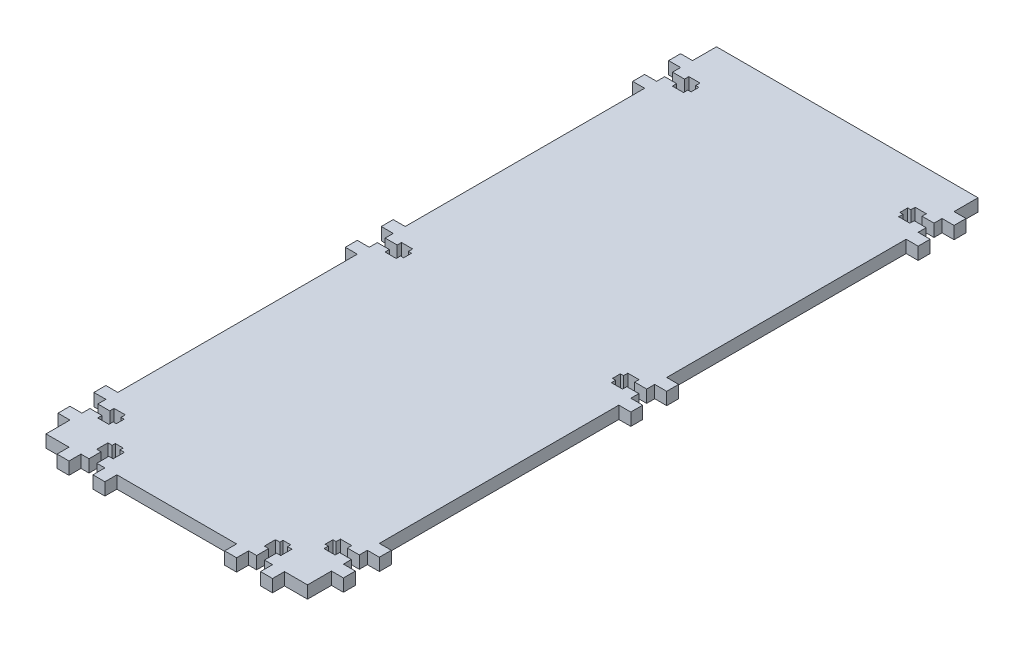
SolidWorks part; units mm, degrees
material "Acrylic (Blue)"
ref_plane "Front Plane" through (0, 0, 0) normal (0, 0, 1) x (1, 0, 0)
ref_plane "Top Plane" through (0, 0, 0) normal (0, 1, 0) x (1, 0, 0)
ref_plane "Right Plane" through (0, 0, 0) normal (1, 0, 0) x (0, 0, -1)
sketch "Sketch1" plane through (0, 0, 0) normal (0, 1, 0) x (1, 0, 0)
  line L0 (-69.342, 177.8) -> (69.342, -177.8) construction
  line L1 (-69.342, 177.8) -> (69.342, 177.8)
  line L2 (-69.342, 177.8) -> (-69.342, -177.8)
  line L3 (-69.342, -177.8) -> (69.342, -177.8)
  line L4 (69.342, 177.8) -> (69.342, -177.8)
  dimension "D1" = 138.684
  dimension "D2" = 355.6
extrude "Boss-Extrude1" add sketch "Sketch1" along normal blind 6.604
sketch "Sketch2" plane through (0, 6.604, 0) normal (0, 1, 0) x (1, 0, 0)
  line L0 (-69.342, 177.8) -> (-69.342, -177.8) construction
  line L1 (69.342, -177.8) -> (69.342, 177.8) construction
  line L2 (-69.342, -177.8) -> (69.342, -177.8) construction
  line L3 (69.342, 177.8) -> (-69.342, 177.8) construction
  line L4 (-75.692, 139.7) -> (-75.692, 12.7) construction
  line L5 (-75.692, -139.7) -> (-75.692, -12.7) construction
  line L6 (-69.342, -177.8) -> (-57.15, -177.8) construction
  line L7 (57.15, -177.8) -> (69.342, -177.8) construction
  line B0 (-69.342, 150.3172) -> (-62.992, 150.3172) construction
  line B1 (-62.992, 150.3172) -> (-62.992, 148.0312) construction
  line B2 (-62.992, 148.0312) -> (-57.0484, 148.0312) construction
  line B3 (-57.0484, 148.0312) -> (-57.0484, 150.3172) construction
  line B4 (-57.0484, 150.3172) -> (-55.372, 150.3172) construction
  line B5 (-55.372, 150.3172) -> (-55.372, 154.4828) construction
  line B6 (-55.372, 154.4828) -> (-57.0484, 154.4828) construction
  line B7 (-57.0484, 154.4828) -> (-57.0484, 156.7688) construction
  line B8 (-57.0484, 156.7688) -> (-62.992, 156.7688) construction
  line B9 (-62.992, 156.7688) -> (-62.992, 154.4828) construction
  line B10 (-62.992, 154.4828) -> (-69.342, 154.4828) construction
  line B11 (-69.342, 154.4828) -> (-69.342, 158.75) construction
  line B12 (-69.342, 158.75) -> (-75.692, 158.75) construction
  line B13 (-75.692, 158.75) -> (-75.692, 165.1) construction
  line B14 (-75.692, 165.1) -> (-69.342, 165.1) construction
  line B15 (-69.342, 150.3172) -> (-69.342, 146.05) construction
  line B16 (-69.342, 146.05) -> (-75.692, 146.05) construction
  line B17 (-75.692, 146.05) -> (-75.692, 139.7) construction
  line B18 (-75.692, 139.7) -> (-69.342, 139.7) construction
  line B19 (-69.342, 154.4828) -> (-69.342, 150.3172) construction
  line B20 (-69.342, -2.0828) -> (-62.992, -2.0828) construction
  line B21 (-62.992, -2.0828) -> (-62.992, -4.3688) construction
  line B22 (-62.992, -4.3688) -> (-57.0484, -4.3688) construction
  line B23 (-57.0484, -4.3688) -> (-57.0484, -2.0828) construction
  line B24 (-57.0484, -2.0828) -> (-55.372, -2.0828) construction
  line B25 (-55.372, -2.0828) -> (-55.372, 2.0828) construction
  line B26 (-55.372, 2.0828) -> (-57.0484, 2.0828) construction
  line B27 (-57.0484, 2.0828) -> (-57.0484, 4.3688) construction
  line B28 (-57.0484, 4.3688) -> (-62.992, 4.3688) construction
  line B29 (-62.992, 4.3688) -> (-62.992, 2.0828) construction
  line B30 (-62.992, 2.0828) -> (-69.342, 2.0828) construction
  line B31 (-69.342, 2.0828) -> (-69.342, 6.35) construction
  line B32 (-69.342, 6.35) -> (-75.692, 6.35) construction
  line B33 (-75.692, 6.35) -> (-75.692, 12.7) construction
  line B34 (-75.692, 12.7) -> (-69.342, 12.7) construction
  line B35 (-69.342, -6.35) -> (-75.692, -6.35) construction
  line B36 (-75.692, -6.35) -> (-75.692, -12.7) construction
  line B37 (-75.692, -12.7) -> (-69.342, -12.7) construction
  line B38 (-69.342, 2.0828) -> (-69.342, -2.0828) construction
  line B39 (-69.342, -154.4828) -> (-62.992, -154.4828) construction
  line B40 (-62.992, -154.4828) -> (-62.992, -156.7688) construction
  line B41 (-62.992, -156.7688) -> (-57.0484, -156.7688) construction
  line B42 (-57.0484, -156.7688) -> (-57.0484, -154.4828) construction
  line B43 (-57.0484, -154.4828) -> (-55.372, -154.4828) construction
  line B44 (-55.372, -154.4828) -> (-55.372, -150.3172) construction
  line B45 (-55.372, -150.3172) -> (-57.0484, -150.3172) construction
  line B46 (-57.0484, -150.3172) -> (-57.0484, -148.0312) construction
  line B47 (-57.0484, -148.0312) -> (-62.992, -148.0312) construction
  line B48 (-62.992, -148.0312) -> (-62.992, -150.3172) construction
  line B49 (-62.992, -150.3172) -> (-69.342, -150.3172) construction
  line B50 (-69.342, -150.3172) -> (-69.342, -146.05) construction
  line B51 (-69.342, -146.05) -> (-75.692, -146.05) construction
  line B52 (-75.692, -146.05) -> (-75.692, -139.7) construction
  line B53 (-75.692, -139.7) -> (-69.342, -139.7) construction
  line B54 (-69.342, -154.4828) -> (-69.342, -158.75) construction
  line B55 (-69.342, -158.75) -> (-75.692, -158.75) construction
  line B56 (-75.692, -158.75) -> (-75.692, -165.1) construction
  line B57 (-75.692, -165.1) -> (-69.342, -165.1) construction
  line B58 (-69.342, -150.3172) -> (-69.342, -154.4828) construction
  line B59 (69.342, 154.4828) -> (62.992, 154.4828) construction
  line B60 (62.992, 154.4828) -> (62.992, 156.7688) construction
  line B61 (62.992, 156.7688) -> (57.0484, 156.7688) construction
  line B62 (57.0484, 156.7688) -> (57.0484, 154.4828) construction
  line B63 (57.0484, 154.4828) -> (55.372, 154.4828) construction
  line B64 (55.372, 154.4828) -> (55.372, 150.3172) construction
  line B65 (55.372, 150.3172) -> (57.0484, 150.3172) construction
  line B66 (57.0484, 150.3172) -> (57.0484, 148.0312) construction
  line B67 (57.0484, 148.0312) -> (62.992, 148.0312) construction
  line B68 (62.992, 148.0312) -> (62.992, 150.3172) construction
  line B69 (62.992, 150.3172) -> (69.342, 150.3172) construction
  line B70 (69.342, 146.05) -> (75.692, 146.05) construction
  line B71 (75.692, 146.05) -> (75.692, 139.7) construction
  line B72 (75.692, 139.7) -> (69.342, 139.7) construction
  line B73 (69.342, 158.75) -> (75.692, 158.75) construction
  line B74 (75.692, 158.75) -> (75.692, 165.1) construction
  line B75 (75.692, 165.1) -> (69.342, 165.1) construction
  line B76 (69.342, 150.3172) -> (69.342, 154.4828) construction
  line B77 (69.342, 2.0828) -> (62.992, 2.0828) construction
  line B78 (62.992, 2.0828) -> (62.992, 4.3688) construction
  line B79 (62.992, 4.3688) -> (57.0484, 4.3688) construction
  line B80 (57.0484, 4.3688) -> (57.0484, 2.0828) construction
  line B81 (57.0484, 2.0828) -> (55.372, 2.0828) construction
  line B82 (55.372, 2.0828) -> (55.372, -2.0828) construction
  line B83 (55.372, -2.0828) -> (57.0484, -2.0828) construction
  line B84 (57.0484, -2.0828) -> (57.0484, -4.3688) construction
  line B85 (57.0484, -4.3688) -> (62.992, -4.3688) construction
  line B86 (62.992, -4.3688) -> (62.992, -2.0828) construction
  line B87 (62.992, -2.0828) -> (69.342, -2.0828) construction
  line B88 (69.342, -6.35) -> (75.692, -6.35) construction
  line B89 (75.692, -6.35) -> (75.692, -12.7) construction
  line B90 (75.692, -12.7) -> (69.342, -12.7) construction
  line B91 (69.342, 2.0828) -> (69.342, 6.35) construction
  line B92 (69.342, 6.35) -> (75.692, 6.35) construction
  line B93 (75.692, 6.35) -> (75.692, 12.7) construction
  line B94 (75.692, 12.7) -> (69.342, 12.7) construction
  line B95 (69.342, -2.0828) -> (69.342, 2.0828) construction
  line B96 (69.342, -150.3172) -> (62.992, -150.3172) construction
  line B97 (62.992, -150.3172) -> (62.992, -148.0312) construction
  line B98 (62.992, -148.0312) -> (57.0484, -148.0312) construction
  line B99 (57.0484, -148.0312) -> (57.0484, -150.3172) construction
  line B100 (57.0484, -150.3172) -> (55.372, -150.3172) construction
  line B101 (55.372, -150.3172) -> (55.372, -154.4828) construction
  line B102 (55.372, -154.4828) -> (57.0484, -154.4828) construction
  line B103 (57.0484, -154.4828) -> (57.0484, -156.7688) construction
  line B104 (57.0484, -156.7688) -> (62.992, -156.7688) construction
  line B105 (62.992, -156.7688) -> (62.992, -154.4828) construction
  line B106 (62.992, -154.4828) -> (69.342, -154.4828) construction
  line B107 (69.342, -154.4828) -> (69.342, -158.75) construction
  line B108 (69.342, -158.75) -> (75.692, -158.75) construction
  line B109 (75.692, -158.75) -> (75.692, -165.1) construction
  line B110 (75.692, -165.1) -> (69.342, -165.1) construction
  line B111 (69.342, -146.05) -> (75.692, -146.05) construction
  line B112 (75.692, -146.05) -> (75.692, -139.7) construction
  line B113 (75.692, -139.7) -> (69.342, -139.7) construction
  line B114 (69.342, -154.4828) -> (69.342, -150.3172) construction
  line B115 (46.5328, -177.8) -> (46.5328, -171.45) construction
  line B116 (46.5328, -171.45) -> (48.8188, -171.45) construction
  line B117 (48.8188, -171.45) -> (48.8188, -165.5064) construction
  line B118 (48.8188, -165.5064) -> (46.5328, -165.5064) construction
  line B119 (46.5328, -165.5064) -> (46.5328, -163.83) construction
  line B120 (46.5328, -163.83) -> (42.3672, -163.83) construction
  line B121 (42.3672, -163.83) -> (42.3672, -165.5064) construction
  line B122 (42.3672, -165.5064) -> (40.0812, -165.5064) construction
  line B123 (40.0812, -165.5064) -> (40.0812, -171.45) construction
  line B124 (40.0812, -171.45) -> (42.3672, -171.45) construction
  line B125 (42.3672, -171.45) -> (42.3672, -177.8) construction
  line B126 (42.3672, -177.8) -> (38.1, -177.8) construction
  line B127 (38.1, -177.8) -> (38.1, -184.15) construction
  line B128 (38.1, -184.15) -> (31.75, -184.15) construction
  line B129 (31.75, -184.15) -> (31.75, -177.8) construction
  line B130 (50.8, -177.8) -> (50.8, -184.15) construction
  line B131 (50.8, -184.15) -> (57.15, -184.15) construction
  line B132 (57.15, -184.15) -> (57.15, -177.8) construction
  line B133 (42.3672, -177.8) -> (46.5328, -177.8) construction
  line B134 (-42.3672, -177.8) -> (-42.3672, -171.45) construction
  line B135 (-42.3672, -171.45) -> (-40.0812, -171.45) construction
  line B136 (-40.0812, -171.45) -> (-40.0812, -165.5064) construction
  line B137 (-40.0812, -165.5064) -> (-42.3672, -165.5064) construction
  line B138 (-42.3672, -165.5064) -> (-42.3672, -163.83) construction
  line B139 (-42.3672, -163.83) -> (-46.5328, -163.83) construction
  line B140 (-46.5328, -163.83) -> (-46.5328, -165.5064) construction
  line B141 (-46.5328, -165.5064) -> (-48.8188, -165.5064) construction
  line B142 (-48.8188, -165.5064) -> (-48.8188, -171.45) construction
  line B143 (-48.8188, -171.45) -> (-46.5328, -171.45) construction
  line B144 (-46.5328, -171.45) -> (-46.5328, -177.8) construction
  line B145 (-46.5328, -177.8) -> (-50.8, -177.8) construction
  line B146 (-50.8, -177.8) -> (-50.8, -184.15) construction
  line B147 (-50.8, -184.15) -> (-57.15, -184.15) construction
  line B148 (-57.15, -184.15) -> (-57.15, -177.8) construction
  line B149 (-42.3672, -177.8) -> (-38.1, -177.8) construction
  line B150 (-38.1, -177.8) -> (-38.1, -184.15) construction
  line B151 (-38.1, -184.15) -> (-31.75, -184.15) construction
  line B152 (-31.75, -184.15) -> (-31.75, -177.8) construction
  line B153 (-46.5328, -177.8) -> (-42.3672, -177.8) construction
  dimension "D1" = 88.9
  dimension "D2" = 12.7
  dimension "D4" = 12.7
sketch_block_instance "NUT_HOLE-1"
sketch_block "NUT_HOLE" parameters "D1"=6.35, "D2"=4.1656, "D3"=25.4, "D4"=6.35, "D5"=8.7376, "D6"=5.9436, "D7"=6.35, "D8"=20.32
sketch_block_instance "NUT_HOLE-2"
sketch_block_instance "NUT_HOLE-3"
sketch_block_instance "NUT_HOLE-4"
sketch_block_instance "NUT_HOLE-5"
sketch_block_instance "NUT_HOLE-6"
sketch_block_instance "NUT_HOLE-8"
sketch_block_instance "NUT_HOLE-9"
sketch "Sketch4" plane through (0, 6.604, 0) normal (0, 1, 0) x (1, 0, 0)
  line L0 (-62.992, 154.4828) -> (-69.342, 154.4828) construction
  line L1 (-62.992, 156.7688) -> (-62.992, 154.4828) construction
  line L2 (-57.0484, 156.7688) -> (-62.992, 156.7688) construction
  line L3 (-57.0484, 154.4828) -> (-57.0484, 156.7688) construction
  line L4 (-55.372, 154.4828) -> (-57.0484, 154.4828) construction
  line L5 (-55.372, 150.3172) -> (-55.372, 154.4828) construction
  line L6 (-57.0484, 150.3172) -> (-55.372, 150.3172) construction
  line L7 (-62.992, 148.0312) -> (-57.0484, 148.0312) construction
  line L8 (-69.342, 150.3172) -> (-62.992, 150.3172) construction
  line L9 (-62.992, 150.3172) -> (-62.992, 148.0312) construction
  line L10 (-57.0484, 148.0312) -> (-57.0484, 150.3172) construction
  line L11 (57.0484, 154.4828) -> (55.372, 154.4828) construction
  line L12 (57.0484, 156.7688) -> (57.0484, 154.4828) construction
  line L13 (62.992, 156.7688) -> (57.0484, 156.7688) construction
  line L14 (62.992, 154.4828) -> (62.992, 156.7688) construction
  line L15 (69.342, 154.4828) -> (62.992, 154.4828) construction
  line L16 (62.992, 150.3172) -> (69.342, 150.3172) construction
  line L17 (62.992, 148.0312) -> (62.992, 150.3172) construction
  line L18 (57.0484, 148.0312) -> (62.992, 148.0312) construction
  line L19 (55.372, 150.3172) -> (57.0484, 150.3172) construction
  line L20 (57.0484, 150.3172) -> (57.0484, 148.0312) construction
  line L21 (55.372, 154.4828) -> (55.372, 150.3172) construction
  line L22 (-62.992, 154.4828) -> (-69.342, 154.4828)
  line L23 (-62.992, 156.7688) -> (-62.992, 154.4828)
  line L24 (-57.0484, 156.7688) -> (-62.992, 156.7688)
  line L25 (-57.0484, 154.4828) -> (-57.0484, 156.7688)
  line L26 (-55.372, 154.4828) -> (-57.0484, 154.4828)
  line L27 (-55.372, 150.3172) -> (-55.372, 154.4828)
  line L28 (-57.0484, 150.3172) -> (-55.372, 150.3172)
  line L29 (-62.992, 148.0312) -> (-57.0484, 148.0312)
  line L30 (-69.342, 150.3172) -> (-62.992, 150.3172)
  line L31 (-62.992, 150.3172) -> (-62.992, 148.0312)
  line L32 (-57.0484, 148.0312) -> (-57.0484, 150.3172)
  line L33 (57.0484, 154.4828) -> (55.372, 154.4828)
  line L34 (57.0484, 156.7688) -> (57.0484, 154.4828)
  line L35 (62.992, 156.7688) -> (57.0484, 156.7688)
  line L36 (62.992, 154.4828) -> (62.992, 156.7688)
  line L37 (69.342, 154.4828) -> (62.992, 154.4828)
  line L38 (62.992, 150.3172) -> (69.342, 150.3172)
  line L39 (62.992, 148.0312) -> (62.992, 150.3172)
  line L40 (57.0484, 148.0312) -> (62.992, 148.0312)
  line L41 (55.372, 150.3172) -> (57.0484, 150.3172)
  line L42 (57.0484, 150.3172) -> (57.0484, 148.0312)
  line L43 (55.372, 154.4828) -> (55.372, 150.3172)
  line L44 (-62.992, 2.0828) -> (-69.342, 2.0828) construction
  line L45 (-62.992, 4.3688) -> (-62.992, 2.0828) construction
  line L46 (-57.0484, 4.3688) -> (-62.992, 4.3688) construction
  line L47 (-57.0484, 2.0828) -> (-57.0484, 4.3688) construction
  line L48 (-55.372, 2.0828) -> (-57.0484, 2.0828) construction
  line L49 (-55.372, -2.0828) -> (-55.372, 2.0828) construction
  line L50 (-57.0484, -2.0828) -> (-55.372, -2.0828) construction
  line L51 (-62.992, -4.3688) -> (-57.0484, -4.3688) construction
  line L52 (-57.0484, -4.3688) -> (-57.0484, -2.0828) construction
  line L53 (-62.992, -2.0828) -> (-62.992, -4.3688) construction
  line L54 (-69.342, -2.0828) -> (-62.992, -2.0828) construction
  line L55 (69.342, 2.0828) -> (62.992, 2.0828) construction
  line L56 (62.992, 2.0828) -> (62.992, 4.3688) construction
  line L57 (62.992, 4.3688) -> (57.0484, 4.3688) construction
  line L58 (57.0484, 4.3688) -> (57.0484, 2.0828) construction
  line L59 (57.0484, 2.0828) -> (55.372, 2.0828) construction
  line L60 (55.372, 2.0828) -> (55.372, -2.0828) construction
  line L61 (55.372, -2.0828) -> (57.0484, -2.0828) construction
  line L62 (57.0484, -2.0828) -> (57.0484, -4.3688) construction
  line L63 (57.0484, -4.3688) -> (62.992, -4.3688) construction
  line L64 (62.992, -2.0828) -> (69.342, -2.0828) construction
  line L65 (62.992, -4.3688) -> (62.992, -2.0828) construction
  line L66 (-62.992, 2.0828) -> (-69.342, 2.0828)
  line L67 (-62.992, 4.3688) -> (-62.992, 2.0828)
  line L68 (-57.0484, 4.3688) -> (-62.992, 4.3688)
  line L69 (-57.0484, 2.0828) -> (-57.0484, 4.3688)
  line L70 (-55.372, 2.0828) -> (-57.0484, 2.0828)
  line L71 (-55.372, -2.0828) -> (-55.372, 2.0828)
  line L72 (-57.0484, -2.0828) -> (-55.372, -2.0828)
  line L73 (-62.992, -4.3688) -> (-57.0484, -4.3688)
  line L74 (-57.0484, -4.3688) -> (-57.0484, -2.0828)
  line L75 (-62.992, -2.0828) -> (-62.992, -4.3688)
  line L76 (-69.342, -2.0828) -> (-62.992, -2.0828)
  line L77 (69.342, 2.0828) -> (62.992, 2.0828)
  line L78 (62.992, 2.0828) -> (62.992, 4.3688)
  line L79 (62.992, 4.3688) -> (57.0484, 4.3688)
  line L80 (57.0484, 4.3688) -> (57.0484, 2.0828)
  line L81 (57.0484, 2.0828) -> (55.372, 2.0828)
  line L82 (55.372, 2.0828) -> (55.372, -2.0828)
  line L83 (55.372, -2.0828) -> (57.0484, -2.0828)
  line L84 (57.0484, -2.0828) -> (57.0484, -4.3688)
  line L85 (57.0484, -4.3688) -> (62.992, -4.3688)
  line L86 (62.992, -2.0828) -> (69.342, -2.0828)
  line L87 (62.992, -4.3688) -> (62.992, -2.0828)
  line L88 (-62.992, -150.3172) -> (-69.342, -150.3172) construction
  line L89 (-62.992, -148.0312) -> (-62.992, -150.3172) construction
  line L90 (-57.0484, -148.0312) -> (-62.992, -148.0312) construction
  line L91 (-57.0484, -150.3172) -> (-57.0484, -148.0312) construction
  line L92 (-55.372, -154.4828) -> (-55.372, -150.3172) construction
  line L93 (-55.372, -150.3172) -> (-57.0484, -150.3172) construction
  line L94 (-57.0484, -154.4828) -> (-55.372, -154.4828) construction
  line L95 (-57.0484, -156.7688) -> (-57.0484, -154.4828) construction
  line L96 (-62.992, -156.7688) -> (-57.0484, -156.7688) construction
  line L97 (-62.992, -154.4828) -> (-62.992, -156.7688) construction
  line L98 (-69.342, -154.4828) -> (-62.992, -154.4828) construction
  line L99 (69.342, -150.3172) -> (62.992, -150.3172) construction
  line L100 (62.992, -150.3172) -> (62.992, -148.0312) construction
  line L101 (62.992, -148.0312) -> (57.0484, -148.0312) construction
  line L102 (57.0484, -148.0312) -> (57.0484, -150.3172) construction
  line L103 (57.0484, -150.3172) -> (55.372, -150.3172) construction
  line L104 (55.372, -150.3172) -> (55.372, -154.4828) construction
  line L105 (55.372, -154.4828) -> (57.0484, -154.4828) construction
  line L106 (57.0484, -154.4828) -> (57.0484, -156.7688) construction
  line L107 (57.0484, -156.7688) -> (62.992, -156.7688) construction
  line L108 (62.992, -154.4828) -> (69.342, -154.4828) construction
  line L109 (62.992, -156.7688) -> (62.992, -154.4828) construction
  line L110 (-62.992, -150.3172) -> (-69.342, -150.3172)
  line L111 (-62.992, -148.0312) -> (-62.992, -150.3172)
  line L112 (-57.0484, -148.0312) -> (-62.992, -148.0312)
  line L113 (-57.0484, -150.3172) -> (-57.0484, -148.0312)
  line L114 (-55.372, -154.4828) -> (-55.372, -150.3172)
  line L115 (-55.372, -150.3172) -> (-57.0484, -150.3172)
  line L116 (-57.0484, -154.4828) -> (-55.372, -154.4828)
  line L117 (-57.0484, -156.7688) -> (-57.0484, -154.4828)
  line L118 (-62.992, -156.7688) -> (-57.0484, -156.7688)
  line L119 (-62.992, -154.4828) -> (-62.992, -156.7688)
  line L120 (-69.342, -154.4828) -> (-62.992, -154.4828)
  line L121 (69.342, -150.3172) -> (62.992, -150.3172)
  line L122 (62.992, -150.3172) -> (62.992, -148.0312)
  line L123 (62.992, -148.0312) -> (57.0484, -148.0312)
  line L124 (57.0484, -148.0312) -> (57.0484, -150.3172)
  line L125 (57.0484, -150.3172) -> (55.372, -150.3172)
  line L126 (55.372, -150.3172) -> (55.372, -154.4828)
  line L127 (55.372, -154.4828) -> (57.0484, -154.4828)
  line L128 (57.0484, -154.4828) -> (57.0484, -156.7688)
  line L129 (57.0484, -156.7688) -> (62.992, -156.7688)
  line L130 (62.992, -154.4828) -> (69.342, -154.4828)
  line L131 (62.992, -156.7688) -> (62.992, -154.4828)
  line L132 (69.342, -150.3172) -> (69.342, -154.4828)
  line L133 (69.342, 2.0828) -> (69.342, -2.0828)
  line L134 (69.342, 154.4828) -> (69.342, 150.3172)
  line L135 (-69.342, 154.4828) -> (-69.342, 150.3172)
  line L136 (-69.342, 2.0828) -> (-69.342, -2.0828)
  line L137 (-69.342, -150.3172) -> (-69.342, -154.4828)
  line L138 (-46.5328, -165.5064) -> (-48.8188, -165.5064) construction
  line L139 (-42.3672, -163.83) -> (-46.5328, -163.83) construction
  line L140 (-40.0812, -165.5064) -> (-42.3672, -165.5064) construction
  line L141 (-46.5328, -163.83) -> (-46.5328, -165.5064) construction
  line L142 (-42.3672, -165.5064) -> (-42.3672, -163.83) construction
  line L143 (-48.8188, -171.45) -> (-46.5328, -171.45) construction
  line L144 (-48.8188, -165.5064) -> (-48.8188, -171.45) construction
  line L145 (-46.5328, -171.45) -> (-46.5328, -177.8) construction
  line L146 (-42.3672, -171.45) -> (-40.0812, -171.45) construction
  line L147 (-40.0812, -171.45) -> (-40.0812, -165.5064) construction
  line L148 (-42.3672, -177.8) -> (-42.3672, -171.45) construction
  line L149 (-46.5328, -165.5064) -> (-48.8188, -165.5064)
  line L150 (-42.3672, -163.83) -> (-46.5328, -163.83)
  line L151 (-40.0812, -165.5064) -> (-42.3672, -165.5064)
  line L152 (-46.5328, -163.83) -> (-46.5328, -165.5064)
  line L153 (-42.3672, -165.5064) -> (-42.3672, -163.83)
  line L154 (-48.8188, -171.45) -> (-46.5328, -171.45)
  line L155 (-48.8188, -165.5064) -> (-48.8188, -171.45)
  line L156 (-46.5328, -171.45) -> (-46.5328, -177.8)
  line L157 (-42.3672, -171.45) -> (-40.0812, -171.45)
  line L158 (-40.0812, -171.45) -> (-40.0812, -165.5064)
  line L159 (-42.3672, -177.8) -> (-42.3672, -171.45)
  line L160 (-46.5328, -177.8) -> (-42.3672, -177.8)
  line L161 (48.8188, -165.5064) -> (46.5328, -165.5064) construction
  line L162 (46.5328, -165.5064) -> (46.5328, -163.83) construction
  line L163 (46.5328, -163.83) -> (42.3672, -163.83) construction
  line L164 (42.3672, -163.83) -> (42.3672, -165.5064) construction
  line L165 (42.3672, -165.5064) -> (40.0812, -165.5064) construction
  line L166 (40.0812, -165.5064) -> (40.0812, -171.45) construction
  line L167 (40.0812, -171.45) -> (42.3672, -171.45) construction
  line L168 (42.3672, -171.45) -> (42.3672, -177.8) construction
  line L169 (46.5328, -177.8) -> (46.5328, -171.45) construction
  line L170 (46.5328, -171.45) -> (48.8188, -171.45) construction
  line L171 (48.8188, -171.45) -> (48.8188, -165.5064) construction
  line L172 (48.8188, -165.5064) -> (46.5328, -165.5064)
  line L173 (46.5328, -165.5064) -> (46.5328, -163.83)
  line L174 (46.5328, -163.83) -> (42.3672, -163.83)
  line L175 (42.3672, -163.83) -> (42.3672, -165.5064)
  line L176 (42.3672, -165.5064) -> (40.0812, -165.5064)
  line L177 (40.0812, -165.5064) -> (40.0812, -171.45)
  line L178 (40.0812, -171.45) -> (42.3672, -171.45)
  line L179 (42.3672, -171.45) -> (42.3672, -177.8)
  line L180 (46.5328, -177.8) -> (46.5328, -171.45)
  line L181 (46.5328, -171.45) -> (48.8188, -171.45)
  line L182 (48.8188, -171.45) -> (48.8188, -165.5064)
  line L183 (42.3672, -177.8) -> (46.5328, -177.8)
extrude "Cut-Extrude1" cut sketch "Sketch4" against normal through all
sketch "Sketch5" plane through (0, 6.604, 0) normal (0, 1, 0) x (1, 0, 0)
  line L0 (-75.692, 165.1) -> (-69.342, 165.1) construction
  line L1 (-75.692, 158.75) -> (-75.692, 165.1) construction
  line L2 (-69.342, 158.75) -> (-75.692, 158.75) construction
  line L3 (-69.342, 146.05) -> (-75.692, 146.05) construction
  line L4 (-75.692, 139.7) -> (-69.342, 139.7) construction
  line L5 (-75.692, 146.05) -> (-75.692, 139.7) construction
  line L6 (75.692, 165.1) -> (69.342, 165.1) construction
  line L7 (75.692, 158.75) -> (75.692, 165.1) construction
  line L8 (69.342, 158.75) -> (75.692, 158.75) construction
  line L9 (69.342, 146.05) -> (75.692, 146.05) construction
  line L10 (75.692, 146.05) -> (75.692, 139.7) construction
  line L11 (75.692, 139.7) -> (69.342, 139.7) construction
  line L12 (-75.692, 12.7) -> (-69.342, 12.7) construction
  line L13 (-69.342, 6.35) -> (-75.692, 6.35) construction
  line L14 (-75.692, -6.35) -> (-75.692, -12.7) construction
  line L15 (-75.692, -12.7) -> (-69.342, -12.7) construction
  line L16 (-69.342, -6.35) -> (-75.692, -6.35) construction
  line L17 (-75.692, 6.35) -> (-75.692, 12.7) construction
  line L18 (-75.692, -139.7) -> (-69.342, -139.7) construction
  line L19 (-75.692, -146.05) -> (-75.692, -139.7) construction
  line L20 (-69.342, -158.75) -> (-75.692, -158.75) construction
  line L21 (-75.692, -158.75) -> (-75.692, -165.1) construction
  line L22 (-75.692, -165.1) -> (-69.342, -165.1) construction
  line L23 (-69.342, -146.05) -> (-75.692, -146.05) construction
  line L24 (75.692, -165.1) -> (69.342, -165.1) construction
  line L25 (69.342, -158.75) -> (75.692, -158.75) construction
  line L26 (75.692, -158.75) -> (75.692, -165.1) construction
  line L27 (69.342, -146.05) -> (75.692, -146.05) construction
  line L28 (75.692, -146.05) -> (75.692, -139.7) construction
  line L29 (75.692, -139.7) -> (69.342, -139.7) construction
  line L30 (75.692, -12.7) -> (69.342, -12.7) construction
  line L31 (75.692, -6.35) -> (75.692, -12.7) construction
  line L32 (69.342, -6.35) -> (75.692, -6.35) construction
  line L33 (69.342, 6.35) -> (75.692, 6.35) construction
  line L34 (75.692, 6.35) -> (75.692, 12.7) construction
  line L35 (75.692, 12.7) -> (69.342, 12.7) construction
  line L36 (-75.692, 165.1) -> (-69.342, 165.1)
  line L37 (-75.692, 158.75) -> (-75.692, 165.1)
  line L38 (-69.342, 158.75) -> (-75.692, 158.75)
  line L39 (-69.342, 146.05) -> (-75.692, 146.05)
  line L40 (-75.692, 139.7) -> (-69.342, 139.7)
  line L41 (-75.692, 146.05) -> (-75.692, 139.7)
  line L42 (75.692, 165.1) -> (69.342, 165.1)
  line L43 (75.692, 158.75) -> (75.692, 165.1)
  line L44 (69.342, 158.75) -> (75.692, 158.75)
  line L45 (69.342, 146.05) -> (75.692, 146.05)
  line L46 (75.692, 146.05) -> (75.692, 139.7)
  line L47 (75.692, 139.7) -> (69.342, 139.7)
  line L48 (-75.692, 12.7) -> (-69.342, 12.7)
  line L49 (-69.342, 6.35) -> (-75.692, 6.35)
  line L50 (-75.692, -6.35) -> (-75.692, -12.7)
  line L51 (-75.692, -12.7) -> (-69.342, -12.7)
  line L52 (-69.342, -6.35) -> (-75.692, -6.35)
  line L53 (-75.692, 6.35) -> (-75.692, 12.7)
  line L54 (-75.692, -139.7) -> (-69.342, -139.7)
  line L55 (-75.692, -146.05) -> (-75.692, -139.7)
  line L56 (-69.342, -158.75) -> (-75.692, -158.75)
  line L57 (-75.692, -158.75) -> (-75.692, -165.1)
  line L58 (-75.692, -165.1) -> (-69.342, -165.1)
  line L59 (-69.342, -146.05) -> (-75.692, -146.05)
  line L60 (75.692, -165.1) -> (69.342, -165.1)
  line L61 (69.342, -158.75) -> (75.692, -158.75)
  line L62 (75.692, -158.75) -> (75.692, -165.1)
  line L63 (69.342, -146.05) -> (75.692, -146.05)
  line L64 (75.692, -146.05) -> (75.692, -139.7)
  line L65 (75.692, -139.7) -> (69.342, -139.7)
  line L66 (75.692, -12.7) -> (69.342, -12.7)
  line L67 (75.692, -6.35) -> (75.692, -12.7)
  line L68 (69.342, -6.35) -> (75.692, -6.35)
  line L69 (69.342, 6.35) -> (75.692, 6.35)
  line L70 (75.692, 6.35) -> (75.692, 12.7)
  line L71 (75.692, 12.7) -> (69.342, 12.7)
  line L72 (69.342, 165.1) -> (69.342, 158.75)
  line L73 (69.342, 146.05) -> (69.342, 139.7)
  line L74 (69.342, 12.7) -> (69.342, 6.35)
  line L75 (69.342, -6.35) -> (69.342, -12.7)
  line L76 (69.342, -139.7) -> (69.342, -146.05)
  line L77 (69.342, -158.75) -> (69.342, -165.1)
  line L78 (-57.15, -177.8) -> (-50.8, -177.8)
  line L79 (-69.342, -165.1) -> (-69.342, -158.75)
  line L80 (-69.342, -146.05) -> (-69.342, -139.7)
  line L81 (-69.342, -6.35) -> (-69.342, -12.7)
  line L82 (-69.342, 12.7) -> (-69.342, 6.35)
  line L83 (-69.342, 146.05) -> (-69.342, 139.7)
  line L84 (-69.342, 165.1) -> (-69.342, 158.75)
  line L85 (-38.1, -177.8) -> (-31.75, -177.8)
  line L86 (31.75, -177.8) -> (38.1, -177.8)
  line L87 (50.8, -177.8) -> (57.15, -177.8)
  line L88 (57.15, -184.15) -> (57.15, -177.8) construction
  line L89 (50.8, -184.15) -> (57.15, -184.15) construction
  line L90 (50.8, -177.8) -> (50.8, -184.15) construction
  line L91 (38.1, -177.8) -> (38.1, -184.15) construction
  line L92 (38.1, -184.15) -> (31.75, -184.15) construction
  line L93 (31.75, -184.15) -> (31.75, -177.8) construction
  line L94 (-57.15, -184.15) -> (-57.15, -177.8) construction
  line L95 (-50.8, -177.8) -> (-50.8, -184.15) construction
  line L96 (-50.8, -184.15) -> (-57.15, -184.15) construction
  line L97 (-38.1, -177.8) -> (-38.1, -184.15) construction
  line L98 (-38.1, -184.15) -> (-31.75, -184.15) construction
  line L99 (-31.75, -184.15) -> (-31.75, -177.8) construction
  line L100 (57.15, -184.15) -> (57.15, -177.8)
  line L101 (50.8, -184.15) -> (57.15, -184.15)
  line L102 (50.8, -177.8) -> (50.8, -184.15)
  line L103 (38.1, -177.8) -> (38.1, -184.15)
  line L104 (38.1, -184.15) -> (31.75, -184.15)
  line L105 (31.75, -184.15) -> (31.75, -177.8)
  line L106 (-57.15, -184.15) -> (-57.15, -177.8)
  line L107 (-50.8, -177.8) -> (-50.8, -184.15)
  line L108 (-50.8, -184.15) -> (-57.15, -184.15)
  line L109 (-38.1, -177.8) -> (-38.1, -184.15)
  line L110 (-38.1, -184.15) -> (-31.75, -184.15)
  line L111 (-31.75, -184.15) -> (-31.75, -177.8)
extrude "Boss-Extrude2" add sketch "Sketch5" against normal up to surface (6.604 mm away) up to face at (0, 0, 40.6217)
